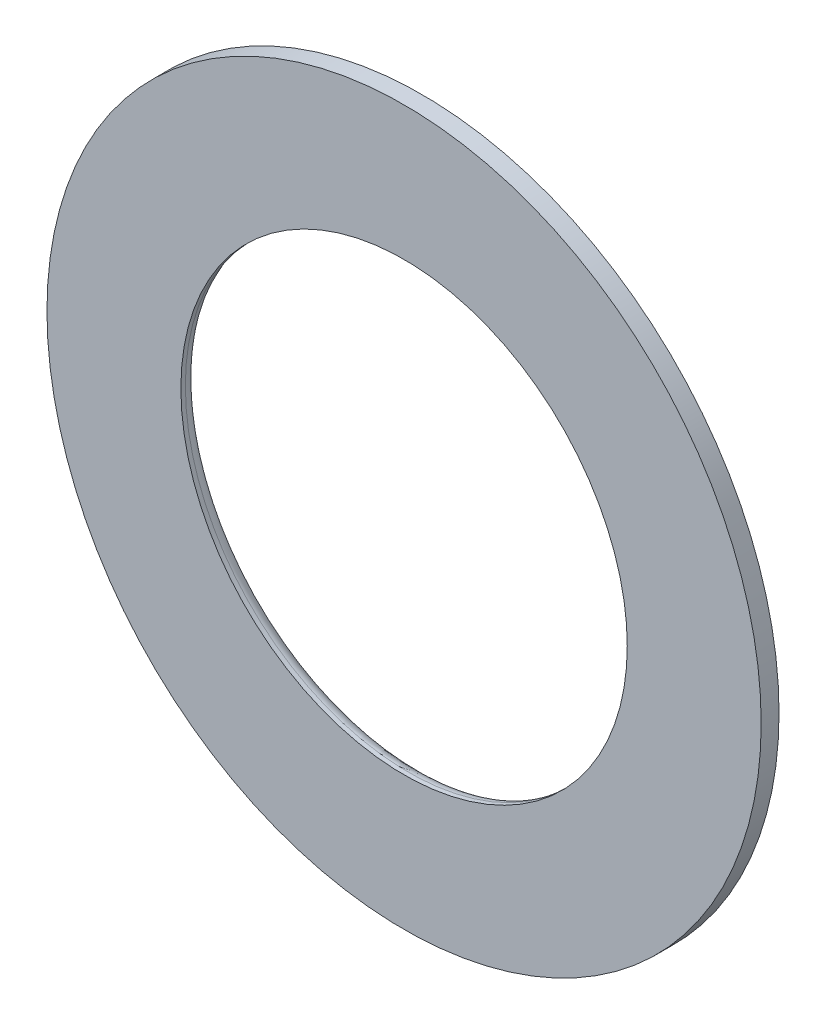
SolidWorks part; units mm, degrees
material "AISI 1010 Steel, hot rolled bar"
ref_plane "Front Plane" through (0, 0, 0) normal (0, 0, 1) x (1, 0, 0)
ref_plane "Top Plane" through (0, 0, 0) normal (0, 1, 0) x (1, 0, 0)
ref_plane "Right Plane" through (0, 0, 0) normal (1, 0, 0) x (0, 0, -1)
sketch "Sketch1" plane through (0, 0, 0) normal (0, 0, 1) x (1, 0, 0)
  circle A0 centre (0, 0) radius 25
  circle A1 centre (0, 0) radius 40
  dimension "D1" = 50
  dimension "D2" = 80
extrude "Boss-Extrude1" add sketch "Sketch1" along normal blind 2
fillet "Fillet2" radius 1.5 1 edges at (25, 0, 0)
